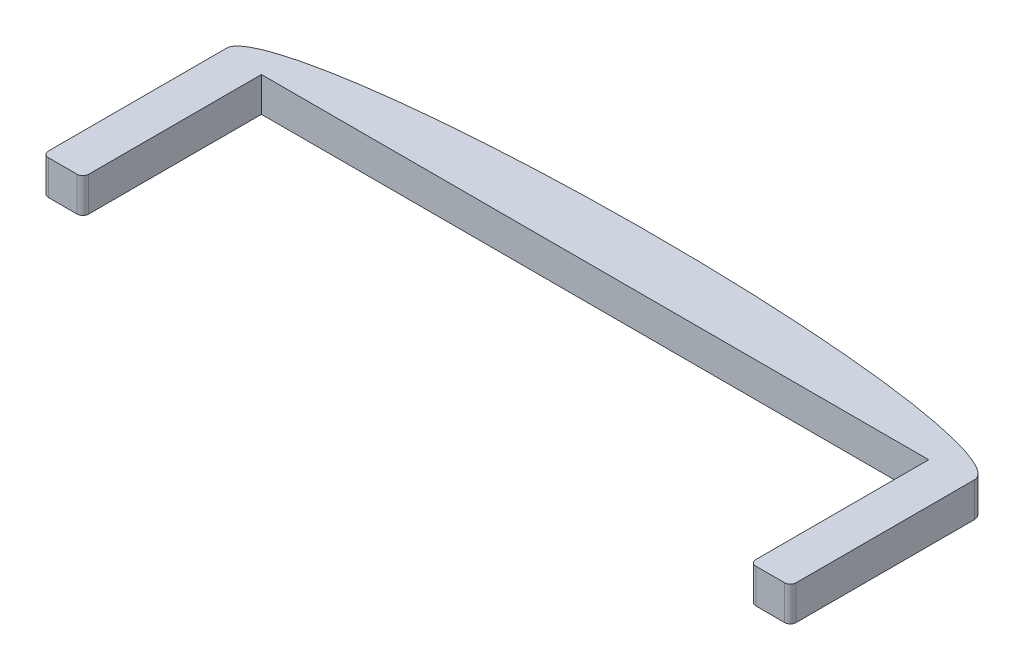
SolidWorks part; units mm, degrees
ref_plane "Front Plane" through (0, 0, 0) normal (0, 0, 1) x (1, 0, 0)
ref_plane "Top Plane" through (0, 0, 0) normal (0, 1, 0) x (1, 0, 0)
ref_plane "Right Plane" through (0, 0, 0) normal (1, 0, 0) x (0, 0, -1)
sketch "Sketch1" plane through (0, 0, 0) normal (0, 1, 0) x (1, 0, 0)
  line L0 (0, 0) -> (-32.5, 0)
  line L1 (-32.5, 0) -> (-32.5, 16)
  line L3 (0, 16) -> (0, 0)
  line L4 (0, 16) -> (0, 20.5)
  ellipse E0 centre (0, 16) end of major axis (-32.5, 16) minor radius 4.5 (0, 20.5) -> (-32.5, 16) ccw
  dimension "D1" = 4.5
  dimension "D2" = 32.5
  dimension "D3" = 16
extrude "Boss-Extrude1" add sketch "Sketch1" along normal blind 3
mirror "Mirror1" about plane through (0, 3, -16) normal (-1, 0, 0) of "Boss-Extrude1"
sketch "Sketch2" plane through (0, 3, 0) normal (0, 1, 0) x (1, 0, 0)
  line L0 (20.26, 10.25) -> (20.26, 0)
  line L1 (-20.26, 10.25) -> (-20.26, 0)
  line L2 (-32.5, 0) -> (32.5, 0) construction
  line L3 (-20.26, 0) -> (20.26, 0)
  line L4 (0, 0) -> (0, 10.25)
  line L5 (0, 10.25) -> (0, 12.5)
  line L6 (-32.5, 16) -> (-32.5, 0) construction
  line L7 (0, 12.5) -> (0, 20.5) construction
  ellipse E0 centre (0, 10.25) end of major axis (-20.26, 10.25) minor radius 2.25 (20.26, 10.25) -> (-20.26, 10.25) ccw
  ellipse E2 centre (0, 16) end of major axis (-32.5, 16) minor radius 4.5 (32.5, 16) -> (-32.5, 16) ccw construction
  line M1 (-32.5, 0) -> (32.5, 0)
  dimension "D1" = 2.25
  dimension "D2" = 12.24
  dimension "D3" = 8
extrude "Cut-Extrude1" cut sketch "Sketch2" against normal through all contours L5 E0 L1 L4 M1 | L0 E0 L5 L4 L3
sketch "Sketch3" plane through (0, 0, 0) normal (0, -1, 0) x (1, 0, 0)
  circle A0 centre (25.46, -4.3615) radius 1.0922 construction
  circle A1 centre (-25.34, -4.3615) radius 1.0922 construction
  circle A2 centre (25.46, -4.3615) radius 1.0922
  circle A3 centre (-25.34, -4.3615) radius 1.0922
extrude "Cut-Extrude2" cut sketch "Sketch3" against normal through all
fillet "Fillet1" radius 5 2 edges at (-20.26, 1.5, 0) (20.26, 1.5, 0)
fillet "Fillet2" radius 0.5 2 edges at (32.5, 1.5, 0) (-32.5, 1.5, 0)
sketch "Sketch4" plane through (0, 0, 0) normal (0, -1, 0) x (1, 0, 0)
  line L2 (0, 0) -> (0, -15.5215) construction
  line L3 (29, -1.8215) -> (29, 0)
  line L4 (29, -1.8215) -> (29, -15.5215)
  line L5 (29, -15.5215) -> (-27.88, -15.5215)
  line L6 (29, -1.8215) -> (29, -15.5215)
  line L7 (29, -15.5215) -> (-29, -15.5215)
  line L8 (25.26, 0) -> (32, 0) construction
  line L9 (29, 0) -> (-29, 0)
  line L10 (-29, -1.8215) -> (-29, -15.5215)
  line L11 (-29, -1.8215) -> (-29, 0)
  dimension "D1" = 1
extrude "Cut-Extrude3" cut sketch "Sketch4" against normal through all
fillet "Fillet3" radius 0.5 2 edges at (-29, 1.5, 0) (29, 1.5, 0)
